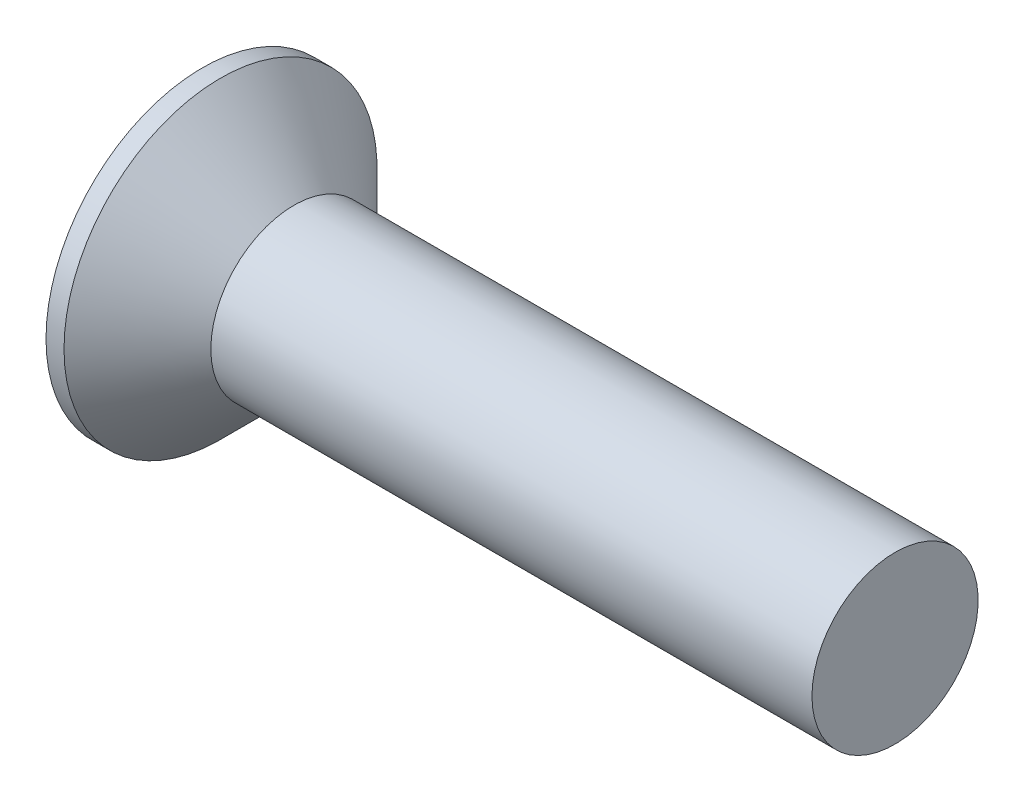
SolidWorks part; units mm, degrees
revolve "Base-Revolve" add sketch "BodySke" angle 360 about L5
sketch "BodySke" plane through (0, 0, 0) normal (0, 0, 1) x (1, 0, 0)
  line L0 (0, 0) -> (0, 5.65)
  line L1 (0, 5.65) -> (0.65, 5.65)
  line L2 (3.3, 3) -> (25, 3)
  line L3 (25, 3) -> (25, 0)
  line L4 (25, 0) -> (0, 0)
  line L5 (-6.35, 0) -> (82.55, 0) construction
  line L6 (3.3, -3) -> (25, -3) construction
  line L7 (0.65, -5.65) -> (3.3, -3) construction
  line L8 (0.65, 5.65) -> (3.3, 3)
  line L9 (0, -5.65) -> (0.65, -5.65) construction
  line L10 (4.3, 4.5875) -> (4.3, -4.9375) construction
  line L11 (0, 6.35) -> (0, -3.175) construction
  dimension "Diameter" = 6
  dimension "Length" = 25
  dimension "Head_ht" = 3.3
  dimension "Head_dia" = 11.3
  dimension "Head_ang" = 90
  dimension "D6" = 0.65
  dimension "Advance" = 1
  dimension "Thread_nom" = 25
cosmetic thread "ThreadCosmetic" [suppressed] parameters "Thread_length"=20.7, "Thread_minor"=4.891
extrude "Slot" [suppressed] cut sketch "Sketch2" against normal blind 1.6
sketch "Sketch2" plane through (0, 0, 0) normal (-1, 0, 0) x (0, 0, 1)
  line L0 (-5.65, -0.95) -> (5.65, -0.95)
  line L1 (-5.65, -0.95) -> (-5.65, 0.95)
  line L2 (5.65, 0.95) -> (-5.65, 0.95)
  line L3 (5.65, 0.95) -> (5.65, -0.95)
  dimension "Slot_width" = 1.9
  dimension "D1" = 0.95
  dimension "D2" = 11.3
  dimension "D3" = 5.65
ref_plane "Plane1" through (0, 0, 0) normal (0, 0, 1) x (1, 0, 0)
ref_plane "Plane2" through (0, 0, 0) normal (0, 1, 0) x (1, 0, 0)
ref_plane "Plane3" through (0, 0, 0) normal (1, 0, 0) x (0, 0, -1)
other "Configuration Table"
sketch "Sketch3" plane through (0, 0, 0) normal (-1, 0, 0) x (0, 0, 1)
  line L0 (-0.56, 3.31) -> (0.56, 3.31)
  line L1 (0.56, 3.31) -> (0.56, -3.31)
  line L2 (0.56, -3.31) -> (-0.56, -3.31)
  line L3 (-0.56, -3.31) -> (-0.56, 3.31)
  dimension "Cross_dia" = 6.62
  dimension "Cross_width" = 1.12
  dimension "D1" = 3.31
  dimension "D2" = 0.56
ref_plane "Plane4" through (3.61, 0, 0) normal (-1, 0, 0) x (0, 0, 1)
sketch "Sketch4" plane through (3.61, 0, 0) normal (-1, 0, 0) x (0, 0, 1)
  line L0 (-0.28, 0.28) -> (0.28, 0.28)
  line L3 (0.28, 0.28) -> (0.28, -0.28)
  line L4 (0.28, -0.28) -> (-0.28, -0.28)
  line L5 (-0.28, -0.28) -> (-0.28, 0.28)
  dimension "D2" = 0.56
  dimension "D1" = 0.56
  dimension "D3" = 0.28
  dimension "D4" = 0.28
loft "Cross" cut profiles "Sketch3", "Sketch4"
pattern_circular "CirPattern1" count 2 every 90 about axis through (0, 0, 0) along (1, 0, 0) of "Cross"
sketch "ThdSchSke" plane through (0, 0, 0) normal (0, 0, 1) x (1, 0, 0)
  line L0 (4.3, -2.4455) -> (3.9117, -3)
  line L1 (4.3, -2.4455) -> (4.6883, -3)
  line L2 (4.6883, -3) -> (4.6883, -3.75)
  line L3 (-3.175, 0) -> (5.1513, 0) construction
  line L5 (4.6883, -3.75) -> (3.9117, -3.75)
  line L6 (3.9117, -3.75) -> (3.9117, -3)
  line L7 (0, 5.65) -> (0, -5.65) construction
  dimension "Diameter" = 6
  dimension "Thread_minor" = 4.891
  dimension "Start" = 4.3
revolve "ThreadSchematic" [suppressed] cut sketch "ThdSchSke" angle 360 about L3
pattern_linear "ThdSchPat" [suppressed]
equation "\"D1@Sketch3\" = \"Cross_dia@Sketch3\" / 2"
equation "\"D2@Sketch3\" = \"Cross_width@Sketch3\" / 2"
equation "\"D1@Sketch4\" = \"Cross_width@Sketch3\" *.5"
equation "\"D2@Sketch4\" = \"D1@Sketch4\""
equation "\"D4@Sketch4\" = \"D2@Sketch4\" / 2"
equation "\"D3@Sketch4\" = \"D1@Sketch4\" / 2"
equation "\"D1@Sketch2\" = \"Slot_width@Sketch2\" / 2"
equation "\"D2@Sketch2\" = \"Head_dia@BodySke\""
equation "\"D3@Sketch2\" = \"D2@Sketch2\" / 2"
equation "\"Thread_length@ThreadCosmetic\" = ((sgn( (\"Length@BodySke\" - \"Advance@BodySke\" - \"Head_ht@BodySke\" ) - \"Thread_nom@BodySke\" )-1)*( (\"Length@BodySke\" - \"Advance@BodySke\" - \"Head_ht@BodySke\" ) - \"Thread_nom@BodySke\" ))/-2+ \"Thread_nom@BodySke\""
equation "\"Thread_minor@ThdSchSke\" = \"Thread_minor@ThreadCosmetic\""
equation "\"Diameter@ThdSchSke\" = \"Diameter@BodySke\""
equation "\"Overcut@ThdSchSke\" = \"Diameter@BodySke\" * 1.25"
equation "\"Start@ThdSchSke\" = 0.000001 + \"Length@BodySke\" - \"Thread_length@ThreadCosmetic\"  '---Countersunk---"
equation "\"Num_threads@ThdSchPat\" = int( \"Thread_length@ThreadCosmetic\" / \"Advance@BodySke\" + 0.999 )  + 1"
equation "\"Advance@ThdSchPat\" = \"Thread_length@ThreadCosmetic\" /  (\"Num_threads@ThdSchPat\" - 1) 'relax it"
